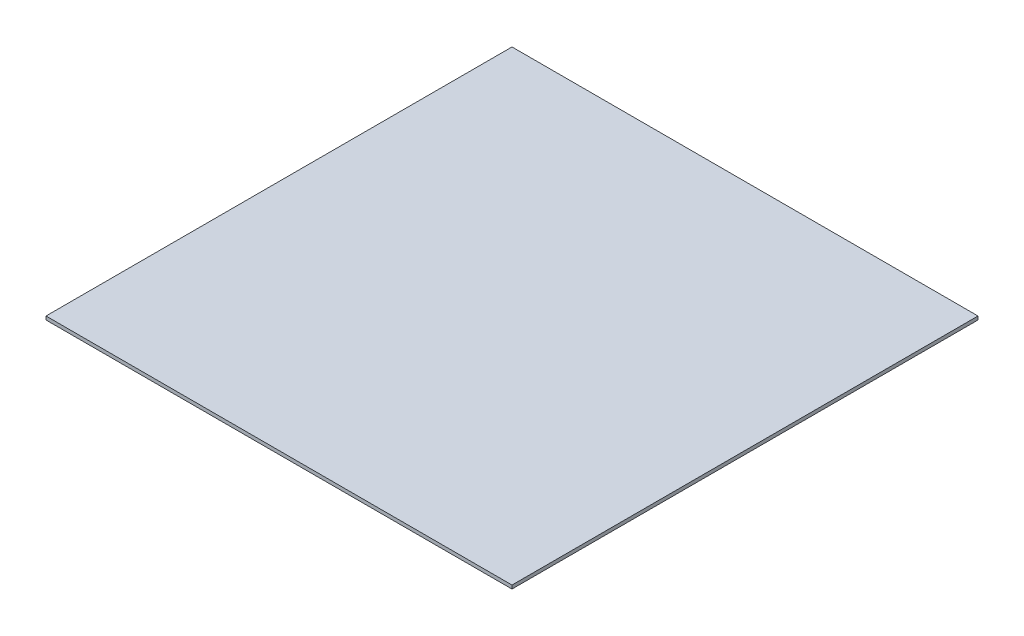
SolidWorks part; units mm, degrees
ref_plane "Front Plane" through (0, 0, 0) normal (0, 0, 1) x (1, 0, 0)
ref_plane "Top Plane" through (0, 0, 0) normal (0, 1, 0) x (1, 0, 0)
ref_plane "Right Plane" through (0, 0, 0) normal (1, 0, 0) x (0, 0, -1)
sketch "Sketch1" plane through (0, 0, 0) normal (0, 1, 0) x (1, 0, 0)
  line L1 (-200, 200) -> (200, 200)
  line L2 (-200, 200) -> (-200, -200)
  line L3 (-200, -200) -> (200, -200)
  line L4 (200, 200) -> (200, -200)
  line L5 (-200, 200) -> (200, -200) construction
  line L6 (-200, -200) -> (200, 200) construction
  point P0 (0, 0)
  dimension "D1" = 400
extrude "Boss-Extrude1" add sketch "Sketch1" along normal blind 3
